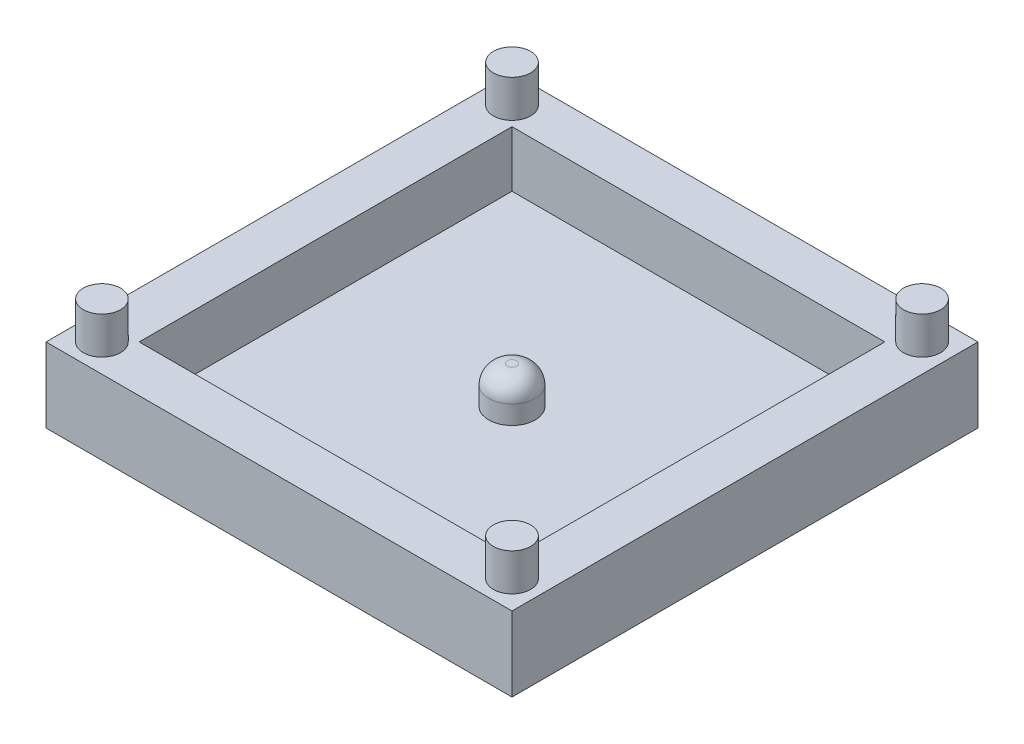
SolidWorks part; units mm, degrees
ref_plane "Front Plane" through (0, 0, 0) normal (0, 0, 1) x (1, 0, 0)
ref_plane "Top Plane" through (0, 0, 0) normal (0, 1, 0) x (1, 0, 0)
ref_plane "Right Plane" through (0, 0, 0) normal (1, 0, 0) x (0, 0, -1)
sketch "Sketch1" plane through (0, 0, 0) normal (0, 1, 0) x (1, 0, 0)
  line L1 (-12.5, -12.5) -> (12.5, -12.5)
  line L2 (-12.5, -12.5) -> (-12.5, 12.5)
  line L3 (-12.5, 12.5) -> (12.5, 12.5)
  line L4 (12.5, -12.5) -> (12.5, 12.5)
  line L5 (-12.5, -12.5) -> (12.5, 12.5) construction
  line L6 (-12.5, 12.5) -> (12.5, -12.5) construction
  point P0 (0, 0)
  dimension "D1" = 25
  dimension "D2" = 25
extrude "Boss-Extrude1" add sketch "Sketch1" along normal blind 4
sketch "Sketch2" plane through (0, 4, 0) normal (0, 1, 0) x (1, 0, 0)
  line L1 (-10, -10) -> (10, -10)
  line L2 (-10, -10) -> (-10, 10)
  line L3 (-10, 10) -> (10, 10)
  line L4 (10, -10) -> (10, 10)
  line L5 (-10, -10) -> (10, 10) construction
  line L6 (-10, 10) -> (10, -10) construction
  point P0 (0, 0)
  dimension "D1" = 20
  dimension "D2" = 20
extrude "Cut-Extrude1" cut sketch "Sketch2" against normal blind 3
sketch "Sketch3" plane through (0, 1, 0) normal (0, 1, 0) x (1, 0, 0)
  circle A0 centre (0, 0) radius 1.25
  dimension "D1" = 2.5
extrude "Boss-Extrude2" add sketch "Sketch3" along normal blind 2
fillet "Fillet1" radius 1 1 edges at (0, 3, 1.25)
sketch "Sketch4" plane through (0, 4, 0) normal (0, 1, 0) x (1, 0, 0)
  line L0 (12.5, 12.5) -> (-12.5, 12.5) construction
  line L1 (-12.5, 12.5) -> (-12.5, -12.5) construction
  line L2 (12.5, -12.5) -> (12.5, 12.5) construction
  line L3 (-12.5, -12.5) -> (12.5, -12.5) construction
  circle A0 centre (-11, 11) radius 1
  circle A1 centre (11, 11) radius 1
  circle A2 centre (11, -11) radius 1
  circle A3 centre (-11, -11) radius 1
  dimension "D1" = 2
  dimension "D4" = 2
  dimension "D7" = 2
  dimension "D10" = 2
  dimension "D2" = 1.5
  dimension "D3" = 1.5
  dimension "D5" = 1.5
  dimension "D6" = 1.5
  dimension "D8" = 1.5
  dimension "D9" = 1.5
  dimension "D11" = 1.5
  dimension "D12" = 1.5
extrude "Boss-Extrude3" add sketch "Sketch4" along normal blind 2
